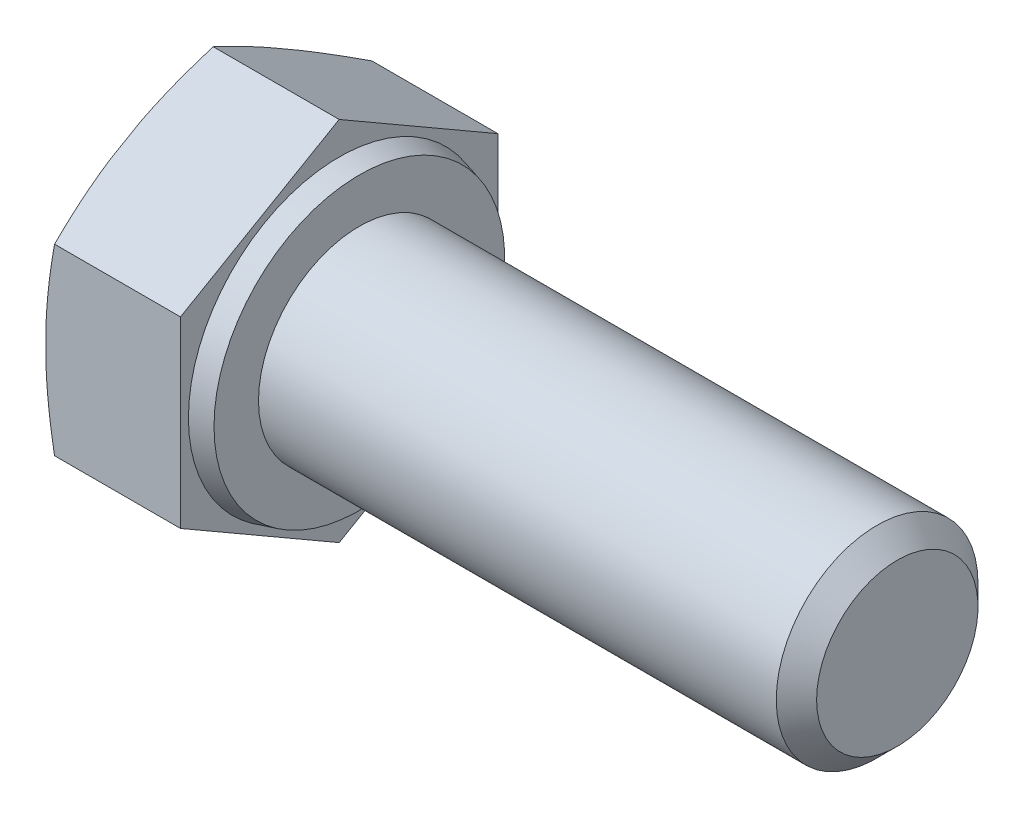
SolidWorks part; units mm, degrees
material "AISI 1020"
ref_plane "Спереди" through (0, 0, 0) normal (0, 0, 1) x (1, 0, 0)
ref_plane "Сверху" through (0, 0, 0) normal (0, 1, 0) x (1, 0, 0)
ref_plane "Справа" through (0, 0, 0) normal (1, 0, 0) x (0, 0, -1)
sketch "Эскиз1" plane through (0, 0, 0) normal (0, 0, 1) x (1, 0, 0)
  line L0 (-1000, 0) -> (49000, 0) construction
  line L1 (-4, 0) -> (-4, 5.45)
  line L2 (-4, 5.45) -> (0, 5.45)
  line L3 (0, 5.45) -> (0, 4.484)
  line L4 (0.6, 3) -> (16.6, 3)
  line L5 (16.6, 3) -> (16.6, 0)
  line L6 (-4, 0) -> (16.6, 0)
  line L7 (0, 4.484) -> (0.6, 4.3232)
  line L8 (0.6, 4.3232) -> (0.6, 3)
  line L9 (0.5, 0) -> (0.5, 4.35) construction
  dimension "_d" = 6
  dimension "D1" = 16
  dimension "D5" = 10.9
  dimension "D2" = 0.6
  dimension "D3" = 4
  dimension "D4" = 0.1
  dimension "D6" = 8.7
  dimension "D7" = 75
revolve "Повернуть1" add sketch "Эскиз1" angle 360 about L0
cosmetic thread "Условное изображение резьбы1" parameters "D2"=4.891
sketch "Эскиз2" plane through (-4, 0, 0) normal (-1, 0, 0) x (0, 0, 1)
  line L1 (0, -5.45) -> (4.7198, -2.725)
  line L2 (4.7198, -2.725) -> (4.7198, 2.725)
  line L3 (4.7198, 2.725) -> (0, 5.45)
  line L4 (0, 5.45) -> (-4.7198, 2.725)
  line L5 (-4.7198, 2.725) -> (-4.7198, -2.725)
  line L6 (-4.7198, -2.725) -> (0, -5.45)
  circle A0 centre (0, 0) radius 4.7198 construction
  circle A1 centre (0, 0) radius 5.45 construction
extrude "Вырез-Вытянуть1" cut sketch "Эскиз2" against normal through all flip side to cut
sketch "Эскиз4" plane through (0, 0, 0) normal (0, 0, 1) x (1, 0, 0)
  line L0 (-1000, 0) -> (49000, 0) construction
  line L1 (-4, 4.75) -> (-3.7452, 5.45)
  line L2 (-3.7452, 5.45) -> (-4, 5.45)
  line L3 (-4, 5.45) -> (-4, 4.75)
  line L4 (-4, 2.725) -> (-4, 5.45) construction
  line L6 (0, 5.45) -> (-4, 5.45) construction
  dimension "D1" = 20
  dimension "D2" = 9.5
revolve "Вырез-Повернуть1" cut sketch "Эскиз4" angle 360 about L0
chamfer "Фаска1" distance 0.6 angle 45 1 edges at (16.6, 0, 3)
equation "\"l\" = 16'длина болта"
equation "\"_d\" = 6'диаметр болта"
equation "\"b\" = 16'длина резьбы"
equation "\"k\" = 4'толщина шляпки"
equation "\"e\" = 10.9'диаметр головки описанный"
equation "\"S\" = 10'размер под ключ"
equation "\"_d@Эскиз1\"=\"_d\""
equation "\"dw\" = 8.7"
equation "\"da\"= 9.78"
equation "\"с\"= 0.6"
equation "\"D1@Эскиз1\"=\"l\""
equation "\"D5@Эскиз1\"=\"e\""
equation "\"D2@Эскиз1\"=\"с\""
equation "\"D3@Эскиз1\"=\"k\""
equation "\"D2@Эскиз4\"=\"S\"*0.95"
equation "\"D1@Фаска1\"=\"_d\"/10"
equation "\"D6@Эскиз1\"=\"dw\""
